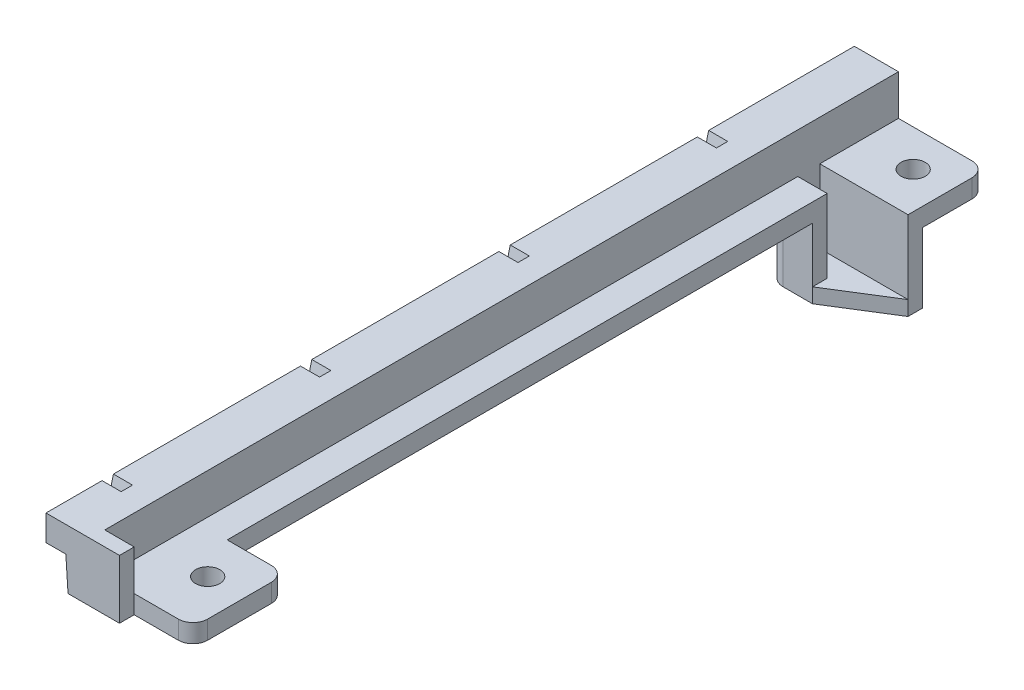
SolidWorks part; units mm, degrees
ref_plane "Front Plane" through (0, 0, 0) normal (0, 0, 1) x (1, 0, 0)
ref_plane "Top Plane" through (0, 0, 0) normal (0, 1, 0) x (1, 0, 0)
ref_plane "Right Plane" through (0, 0, 0) normal (1, 0, 0) x (0, 0, -1)
sketch "Side lip main section" plane through (0, 0, 0) normal (0, 1, 0) x (1, 0, 0)
  line L1 (0, 0) -> (6, 0)
  line L2 (0, 0) -> (0, -108)
  line L3 (0, -108) -> (6, -108)
  line L4 (6, 0) -> (6, -108)
  dimension "D1" = 6
  dimension "D2" = 108
extrude "Side lip" add sketch "Side lip main section" against normal blind 5
sketch "Sketch2" plane through (0, 0, 0) normal (-1, 0, 0) x (0, 0, 1)
  line L0 (102, 0) -> (103.2466, -5)
  line L1 (0, 0) -> (108, 0) construction
  line L2 (0, -5) -> (108, -5) construction
  line L3 (100.4541, 0) -> (101.7007, -5)
  line L4 (75, 0) -> (76.2466, -5)
  line L5 (73.4541, 0) -> (74.7007, -5)
  line L6 (48, 0) -> (49.2466, -5)
  line L7 (46.4541, 0) -> (47.7007, -5)
  line L8 (21, 0) -> (22.2466, -5)
  line L9 (19.4541, 0) -> (20.7007, -5)
  line L10 (21, 0) -> (19.5446, -0.3629) construction
  line L11 (48, 0) -> (46.5446, -0.3629) construction
  line L12 (75, 0) -> (73.5446, -0.3629) construction
  line L13 (102, 0) -> (100.5446, -0.3629) construction
  line L14 (102, 0) -> (102, -5) construction
  line L15 (108, -5) -> (108, 0) construction
  line L16 (75, 0) -> (75, -5) construction
  line L17 (48, 0) -> (48, -5) construction
  line L18 (21, 0) -> (21, -5) construction
  line L19 (19.4541, 0) -> (21, 0)
  line L20 (20.7007, -5) -> (22.2466, -5)
  line L21 (47.7007, -5) -> (49.2466, -5)
  line L22 (46.4541, 0) -> (48, 0)
  line L23 (73.4541, 0) -> (75, 0)
  line L24 (74.7007, -5) -> (76.2466, -5)
  line L25 (100.4541, 0) -> (102, 0)
  line L26 (101.7007, -5) -> (103.2466, -5)
  dimension "D1" = 1.5
  dimension "D2" = 76
  dimension "D3" = 6
  dimension "D4" = 27
  dimension "D5" = 54
  dimension "D6" = 81
extrude "Vertical fin cuts" cut sketch "Sketch2" against normal blind 2.6
sketch "Sketch4" plane through (0, -5, 0) normal (0, -1, 0) x (1, 0, 0)
  line L0 (6, 0) -> (0, 0) construction
  line L1 (6, 108) -> (2.5, 108)
  line L2 (6, 108) -> (6, 0)
  line L3 (6, 0) -> (2.5, 0)
  line L4 (2.5, 108) -> (2.5, 0)
  dimension "D1" = 3.5
extrude "Descender" add sketch "Sketch4" along normal blind 4.5
sketch "Sketch5" plane through (6, 0, 0) normal (1, 0, 0) x (0, 0, -1)
  line L0 (0, -9.5) -> (0, 0) construction
  line L1 (-108, -9.5) -> (0, -9.5)
  line L2 (-108, -9.5) -> (-108, -7)
  line L3 (-108, -7) -> (0, -7)
  line L4 (0, -9.5) -> (0, -7)
  dimension "D1" = 2.5
extrude "PCB base" add sketch "Sketch5" along normal blind 4
sketch "Sketch8" plane through (0, 0, 108) normal (0, 0, 1) x (1, 0, 0)
  line L1 (6, 0) -> (10, 0)
  line L4 (10, 0) -> (10, -7)
  line L8 (6, 0) -> (0, 0)
  line L9 (0, 0) -> (0, -5)
  line L10 (0, -5) -> (2.5, -5)
  line L11 (2.5, -5) -> (2.5, -9.5)
  line L12 (2.5, -9.5) -> (10, -9.5)
  line L13 (10, -9.5) -> (10, -7)
  line L14 (10, -7) -> (6, -7)
  line L15 (6, -7) -> (6, 0)
  line L16 (6, 0) -> (0, 0)
  line L17 (0, 0) -> (0, -5)
  line L18 (0, -5) -> (2.5, -5)
  line L19 (2.5, -5) -> (2.5, -9.5)
  line L20 (2.5, -9.5) -> (10, -9.5)
  line L21 (10, -9.5) -> (10, -7)
  dimension "D1" = 0
extrude "Lower cap" add sketch "Sketch8" along normal blind 2
sketch "Sketch9" plane through (10, 0, 0) normal (1, 0, 0) x (0, 0, -1)
  line L0 (0, -7) -> (-108, -7) construction
  line L1 (-13.7, -7) -> (-10.7, -7)
  line L2 (-13.7, -7) -> (-13.7, -9.5)
  line L3 (-13.7, -9.5) -> (-10.7, -9.5)
  line L4 (-10.7, -7) -> (-10.7, -9.5)
  line L5 (-110, -9.5) -> (0, -9.5) construction
  line L6 (-108, -7) -> (-108, 0) construction
  dimension "D1" = 94.3
  dimension "D2" = 3
extrude "Al bar cut" cut sketch "Sketch9" against normal blind 4
sketch "Sketch10" plane through (10, 0, 0) normal (1, 0, 0) x (0, 0, -1)
  line L0 (-110, -9.5) -> (-13.7, -9.5) construction
  line L1 (-108, -7) -> (-95.3463, -7)
  line L2 (-108, -7) -> (-108, -9.5)
  line L3 (-108, -9.5) -> (-95.3463, -9.5)
  line L4 (-95.3463, -7) -> (-95.3463, -9.5)
  line L6 (-10.7, -7) -> (0, -7)
  line L7 (-10.7, -7) -> (-10.7, -9.5)
  line L8 (-10.7, -9.5) -> (0, -9.5)
  line L9 (0, -7) -> (0, -9.5)
extrude "Support tabs" add sketch "Sketch10" along normal blind 8
sketch "Sketch11" plane through (0, -7, 0) normal (0, 1, 0) x (1, 0, 0)
  line L0 (13, 0) -> (13, -108) construction
  line L5 (18, 0) -> (6, 0) construction
  line L6 (18, -108) -> (10, -108) construction
  line L7 (6, 0) -> (6, -10.7) construction
  line L8 (6, -101) -> (18, -101) construction
  line L9 (6, -13.7) -> (6, -108) construction
  line L10 (18, -95.3463) -> (18, -108) construction
  line L11 (6, -5) -> (18, -5) construction
  line L12 (18, 0) -> (18, -10.7) construction
  circle A0 centre (13, -5) radius 1.65
  circle A1 centre (13, -101) radius 1.65
  dimension "D4" = 3.3
  dimension "D1" = 7
  dimension "D2" = 7
  dimension "D3" = 103
extrude "Bolt holes" cut sketch "Sketch11" against normal up to next
sketch "Sketch12" plane through (0, -9.5, 0) normal (0, -1, 0) x (1, 0, 0)
  line L0 (6, 10.7) -> (18, 10.7) construction
  line L1 (6, 13.7) -> (6, 10.7) construction
  line L2 (6, 13.7) -> (10, 13.7) construction
  line L3 (6, 10.7) -> (18, 10.7)
  line L4 (6, 13.7) -> (6, 10.7)
  line L5 (6, 13.7) -> (10, 13.7)
  line L6 (4, 15.7) -> (10, 15.7)
  line L7 (4, 15.7) -> (4, 8.7)
  line L8 (4, 8.7) -> (18, 8.7)
  line L9 (10, 15.7) -> (10, 13.7)
  line L10 (18, 10.7) -> (18, 8.7)
  dimension "D1" = 2
extrude "Al bar enclosure" add sketch "Sketch12" along normal blind 7.5
sketch "Sketch13" plane through (0, -17, 0) normal (0, -1, 0) x (1, 0, 0)
  line L1 (10, 15.7) -> (4, 15.7) construction
  line L2 (4, 15.7) -> (4, 8.7) construction
  line L3 (4, 8.7) -> (18, 8.7) construction
  line L4 (18, 8.7) -> (18, 10.7) construction
  line L6 (10, 15.7) -> (4, 15.7)
  line L7 (4, 15.7) -> (4, 8.7)
  line L8 (4, 8.7) -> (18, 8.7)
  line L9 (18, 8.7) -> (18, 10.7)
  line L10 (18, 10.7) -> (10, 15.7)
extrude "Al bar base" add sketch "Sketch13" along normal blind 2 contours L10 L6 L7 L8 L9
fillet "Fillet1" radius 2 5 edges at (4, -14.25, 8.7) (4, -14.25, 15.7) (18, -8.25, 95.3463) (18, -8.25, 108) (18, -8.25, 0)
sketch "Sketch16" plane through (0, 0, 110) normal (0, 0, 1) x (1, 0, 0)
  line L0 (10, -9.5) -> (10, 0) construction
  line L1 (0, 0) -> (10, 0)
  line L2 (0, 0) -> (0, -0.5)
  line L3 (0, -0.5) -> (10, -0.5)
  line L4 (10, 0) -> (10, -0.5)
  dimension "D1" = 0.5
extrude "Reduce side support height" cut sketch "Sketch16" against normal through all
sketch "Sketch17" plane through (0, 0, 110) normal (0, 0, 1) x (1, 0, 0)
  line L0 (2.5, -5) -> (2.7, -5)
  line L1 (2.7, -5) -> (3, -9.5)
  line L2 (2.5, -9.5) -> (10, -9.5) construction
  line L3 (3, -9.5) -> (2.5, -9.5)
  line L4 (2.5, -9.5) -> (2.5, -5)
  dimension "D1" = 0.2
  dimension "D2" = 0.5
extrude "Sit flat!" cut sketch "Sketch17" against normal through all
sketch "Sketch19" plane through (0, 0, 0) normal (-1, 0, 0) x (0, 0, 1)
  line L0 (110, -0.5) -> (110, -5) construction
  line L1 (0, -0.5) -> (110, -0.5)
  line L2 (0, -0.5) -> (0, -1.5)
  line L3 (0, -1.5) -> (110, -1.5)
  line L4 (110, -0.5) -> (110, -1.5)
  dimension "D1" = 1
extrude "Lower top" cut sketch "Sketch19" against normal through all
